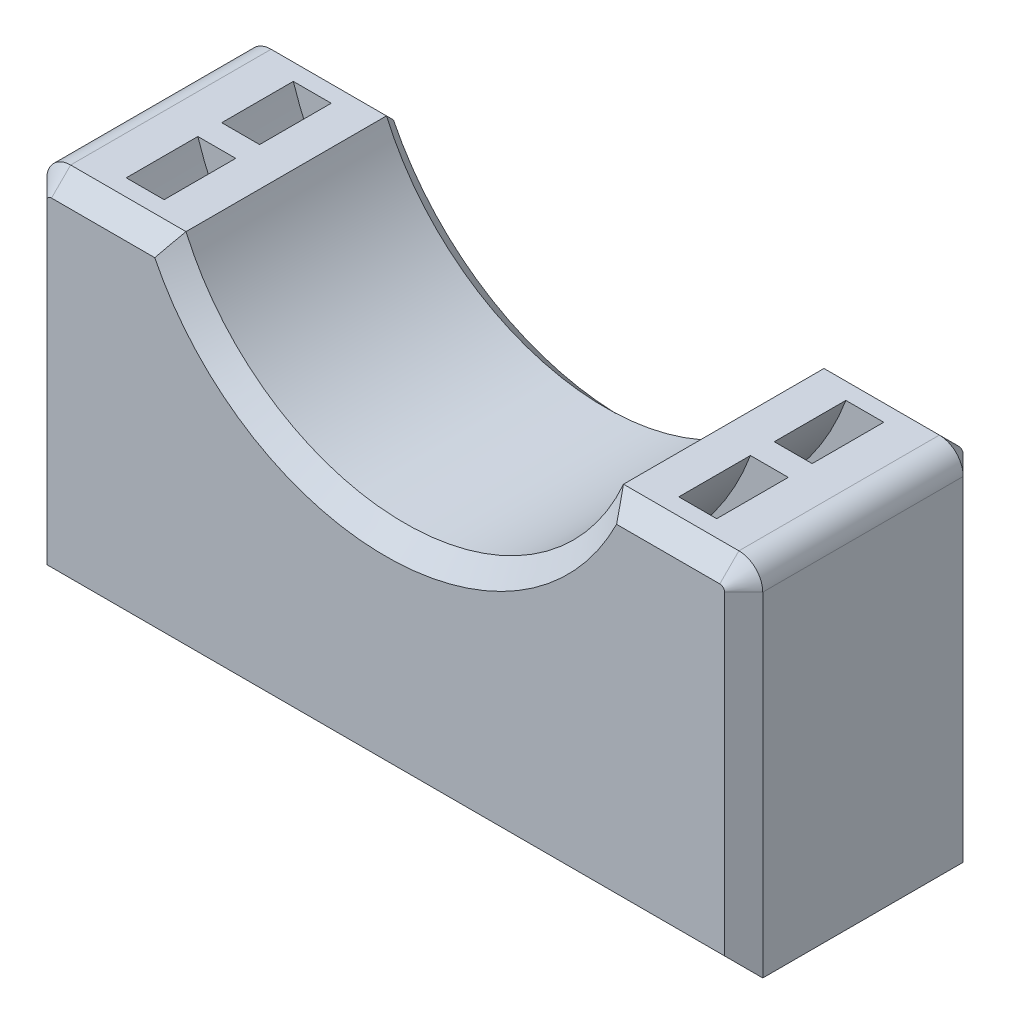
SolidWorks part; units mm, degrees
ref_plane "Front Plane" through (0, 0, 0) normal (0, 0, 1) x (1, 0, 0)
ref_plane "Top Plane" through (0, 0, 0) normal (0, 1, 0) x (1, 0, 0)
ref_plane "Right Plane" through (0, 0, 0) normal (1, 0, 0) x (0, 0, -1)
sketch "Sketch1" plane through (0, 0, 0) normal (0, 0, 1) x (1, 0, 0)
  line L1 (-15, -7.5) -> (15, -7.5)
  line L2 (-15, -7.5) -> (-15, 7.5)
  line L3 (-15, 7.5) -> (15, 7.5)
  line L4 (15, -7.5) -> (15, 7.5)
  line L5 (-15, -7.5) -> (15, 7.5) construction
  line L6 (-15, 7.5) -> (15, -7.5) construction
  circle A0 centre (0, 11.5) radius 10
  point P0 (0, 0)
  point P8 (0, 8.7094)
  dimension "D3" = 20
  dimension "D1" = 15
  dimension "D2" = 30
  dimension "D4" = 4
extrude "Boss-Extrude1" add sketch "Sketch1" along normal blind 10 contours A0 L3 L2 L1 L4
sketch "Sketch2" plane through (0, -7.5, 0) normal (0, -1, 0) x (1, 0, 0)
  line L0 (0, 0) -> (0, 10) construction
  line L1 (-15, 10) -> (15, 10) construction
  line L2 (0, 5) -> (-8, 5) construction
  circle A0 centre (-8, 5) radius 1.4
  circle A1 centre (8, 5) radius 1.4
  dimension "D1" = 2.8
  dimension "D2" = 8
extrude "Cut-Extrude1" cut sketch "Sketch2" against normal blind 6
sketch "Sketch3" plane through (0, 0, 0) normal (1, 0, 0) x (0, 0, -1)
  line L0 (0, 11.5) -> (-10, 11.5) construction
  line L1 (-10, 7.5) -> (-10, 1.5) construction
  line L2 (-10, 11.5) -> (-10, 1.5) construction
  line L3 (0, 21.5) -> (0, 1.5) construction
  line L4 (-8.5, 0) -> (-5.5, 0)
  line L5 (-8.5, 0) -> (-8.5, -1.5)
  line L6 (-8.5, -1.5) -> (-5.5, -1.5)
  line L7 (-5.5, 0) -> (-5.5, -1.5)
  line L8 (-4.5, 0) -> (-1.5, 0)
  line L9 (-4.5, 0) -> (-4.5, -1.5)
  line L10 (-4.5, -1.5) -> (-1.5, -1.5)
  line L11 (-1.5, 0) -> (-1.5, -1.5)
  dimension "D1" = 1.5
  dimension "D2" = 1.5
  dimension "D3" = 3
  dimension "D4" = 1.5
  dimension "D5" = 1.5
revolve "Cut-Revolve1" cut sketch "Sketch3" angle 360 about L0
fillet "Fillet1" radius 1 2 edges at (15, 7.5, 5) (-15, 7.5, 5)
chamfer "Chamfer1" distance 0.8 angle 45 16 edges at (11.5826, 7.5, 0) (-11.5826, 7.5, 0) (-15, -0.5, 0) (0, -7.5, 0) (15, -0.5, 0) (0, 1.5, 0) (11.5826, 7.5, 10) (-11.5826, 7.5, 10) (15, -0.5, 10) (0, -7.5, 10) (-15, -0.5, 10) (0, 1.5, 10) (-14.7071, 7.2071, 0) (14.7071, 7.2071, 0) (-14.7071, 7.2071, 10) (14.7071, 7.2071, 10)
